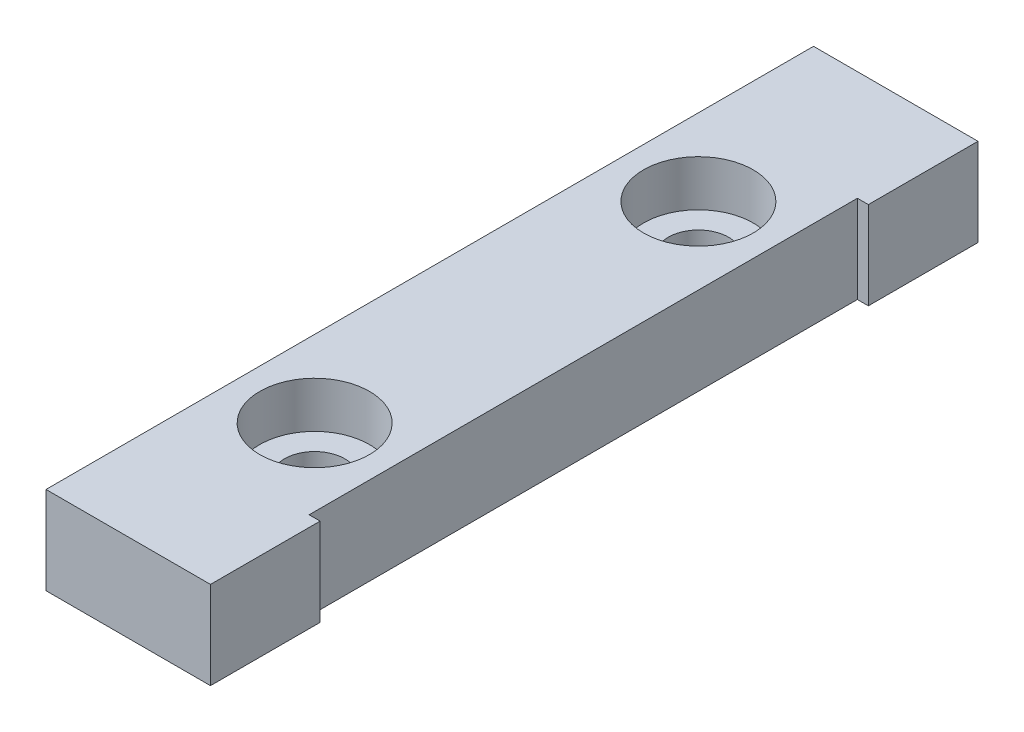
SolidWorks part; units mm, degrees
ref_plane "Front Plane" through (0, 0, 0) normal (0, 0, 1) x (1, 0, 0)
ref_plane "Top Plane" through (0, 0, 0) normal (0, 1, 0) x (1, 0, 0)
ref_plane "Right Plane" through (0, 0, 0) normal (1, 0, 0) x (0, 0, -1)
sketch "Sketch1" plane through (0, 0, 0) normal (0, 1, 0) x (1, 0, 0)
  line L0 (7.5, 25) -> (6.5, 25)
  line L1 (-7.5, -35) -> (7.5, -35)
  line L2 (-7.5, -35) -> (-7.5, 35)
  line L3 (-7.5, 35) -> (7.5, 35)
  line L4 (7.5, -35) -> (7.5, -25)
  line L5 (-7.5, -35) -> (7.5, 35) construction
  line L6 (-7.5, 35) -> (7.5, -35) construction
  line L7 (6.5, 25) -> (6.5, -25)
  line L8 (6.5, -25) -> (7.5, -25)
  line L9 (7.5, 25) -> (7.5, 35)
  point P0 (0, 0)
  dimension "D1" = 15
  dimension "D2" = 70
  dimension "D3" = 10
  dimension "D4" = 10
  dimension "D5" = 1
extrude "Boss-Extrude1" add sketch "Sketch1" along normal blind 8
sketch "Sketch2" plane through (0, 8, 0) normal (0, 1, 0) x (1, 0, 0)
  line L0 (-7.5, 35) -> (-7.5, -35) construction
  circle A0 centre (-0.5, 17.5) radius 2.75
  circle A1 centre (-0.5, -17.5) radius 2.75
  point P4 (0, 0)
  point P8 (0, 0)
  point P9 (0, 0)
  dimension "D1" = 5.5
  dimension "D2" = 5.5
  dimension "D3" = 17.5
  dimension "D4" = 17.5
  dimension "D5" = 7
  dimension "D6" = 7
extrude "Cut-Extrude1" cut sketch "Sketch2" against normal through all contours A1 | A0
sketch "Sketch3" plane through (0, 8, 0) normal (0, 1, 0) x (1, 0, 0)
  circle A0 centre (-0.5, 17.5) radius 5
  circle A1 centre (-0.5, -17.5) radius 5
extrude "Cut-Extrude2" cut sketch "Sketch3" against normal blind 4.2
